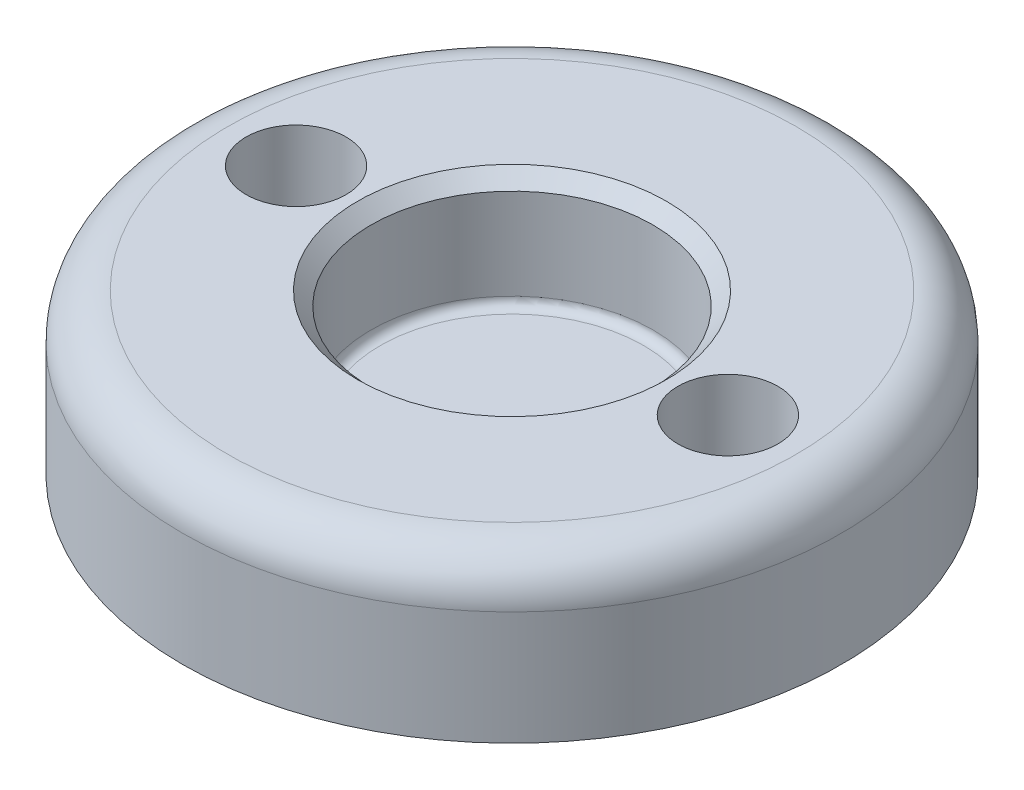
SolidWorks part; units mm, degrees
material "Brass"
ref_plane "Front Plane" through (0, 0, 0) normal (0, 0, 1) x (1, 0, 0)
ref_plane "Top Plane" through (0, 0, 0) normal (0, 1, 0) x (1, 0, 0)
ref_plane "Right Plane" through (0, 0, 0) normal (1, 0, 0) x (0, 0, -1)
sketch "Sketch1" plane through (0, 0, 0) normal (0, 0, 1) x (1, 0, 0)
  line L0 (0, 0) -> (0, 7.0462) construction
  line L1 (0, 0) -> (-7.25, 0)
  line L2 (-7.25, 0) -> (-7.25, 3.5)
  line L3 (-7.25, 3.5) -> (-3.1, 3.5)
  line L4 (-3.1, 3.5) -> (-3.1, 1)
  line L5 (-3.1, 1) -> (0, 1)
  line L6 (0, 0) -> (0, 1)
  dimension "D1" = 3.1
  dimension "D2" = 4.15
  dimension "D3" = 1
  dimension "D4" = 2.5
  dimension "D5" = 7.25
revolve "Revolve1" add sketch "Sketch1" angle 360 about L0
chamfer "Chamfer2" distance 0.3 angle 45 1 edges at (0, 3.5, -3.1)
sketch "Sketch2" plane through (0, 3.5, 0) normal (0, 1, 0) x (1, 0, 0)
  line L0 (-6.8053, -2.5) -> (-12.25, -2.5)
  line L1 (-12.25, -2.5) -> (-12.25, 2.5)
  line L2 (-12.25, 2.5) -> (-6.8053, 2.5)
  line L3 (-12.25, 0) -> (-7.25, 0) construction
  circle A0 centre (0, 0) radius 7.25 construction
  arc A1 (-6.8053, 2.5) -> (-6.8053, -2.5) centre (0, 0) ccw
  point P2 (-12.25, 0)
  dimension "D1" = 5
extrude "Boss-Extrude1" [suppressed] add sketch "Sketch2" against normal up to surface (3 mm away)
hole_wizard "CSK for M2 Flat Head Machine Screw1" positions "Sketch3" profile "Sketch4" countersink size "M2" standard "ANSI Metric"
sketch "Sketch3" plane through (0, 0, 0) normal (0, -1, 0) x (-1, 0, 0)
  point P0 (4.75, 0)
  dimension "D1" = 4.75
sketch "Sketch4" plane through (-4.75, 0, 0) normal (1, 0, 0) x (0, 0, -1)
  line L0 (0, 0) -> (0, 5.6609)
  line L1 (0, 5.6609) -> (1.1, 5)
  line L2 (1.1, 5) -> (1.1, 1.1)
  line L3 (1.1, 1.1) -> (2.2, 0)
  line L5 (2.2, 0) -> (0, 0)
  line L6 (-1.1, 1.1) -> (-2.2, 0) construction
  line L10 (0, 5.6609) -> (-1.1, 5) construction
  line L11 (0, -6.35) -> (0, 107.95) construction
  dimension "Hole Dia." = 2.2
  dimension "Hole Depth" = 5
  dimension "Near C'Sink Dia." = 4.4
  dimension "Near C'Sink Angle" = 90
  dimension "Drill Angle" = 118
sketch "Sketch5" [suppressed] plane through (0, 0, 0) normal (0, -1, 0) x (1, 0, 0)
  line L1 (-6.8053, 2.5) -> (-12.25, 2.5) construction
  line L2 (-6.8053, 2.5) -> (-12.25, 2.5) construction
  line L3 (-12.25, -2.5) -> (-6.8053, -2.5) construction
  line L4 (-4.75, -2.5) -> (-12.25, -2.5)
  line L5 (-12.25, -2.5) -> (-12.25, 2.5)
  line L9 (-12.25, 2.5) -> (-4.75, 2.5)
  arc A0 (-4.75, -2.5) -> (-4.75, 2.5) centre (-4.75, 0) cw
extrude "Cut-Extrude1" [suppressed] cut sketch "Sketch5" against normal through all both and the other way through all
pattern_circular "CirPattern1" count 2 over 360 about axis through (0, 0, 0) along (0, 1, 0) of "CSK for M2 Flat Head Machine Screw1", "Boss-Extrude1", "Cut-Extrude1"
fillet "Fillet1" [suppressed] radius 10
fillet "Fillet2" radius 0.2 1 edges at (0, 1, -3.1)
fillet "Fillet3" radius 1 1 edges at (0, 3.5, -7.25)
